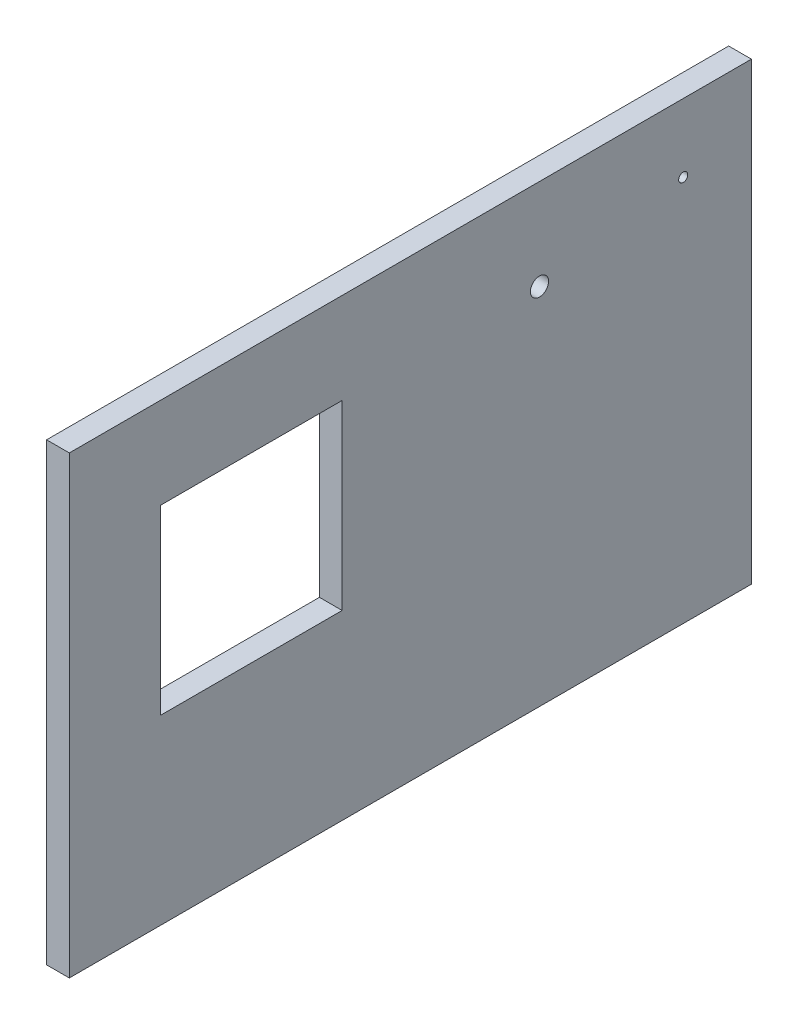
SolidWorks part; units mm, degrees
ref_plane "Front Plane" through (0, 0, 0) normal (0, 0, 1) x (1, 0, 0)
ref_plane "Top Plane" through (0, 0, 0) normal (0, 1, 0) x (1, 0, 0)
ref_plane "Right Plane" through (0, 0, 0) normal (1, 0, 0) x (0, 0, -1)
sketch "Sketch1" plane through (0, 0, 0) normal (1, 0, 0) x (0, 0, -1)
  line L1 (-150, 100) -> (150, 100)
  line L2 (-150, 100) -> (-150, -100)
  line L3 (-150, -100) -> (150, -100)
  line L4 (150, 100) -> (150, -100)
  line L5 (-150, 100) -> (150, -100) construction
  line L6 (-150, -100) -> (150, 100) construction
  point P0 (0, 0)
  dimension "D1" = 300
  dimension "D2" = 200
extrude "Boss-Extrude1" add sketch "Sketch1" along normal blind 10
sketch "Sketch2" plane through (10, 0, 0) normal (1, 0, 0) x (0, 0, -1)
  line L0 (120, 100) -> (120, 70) construction
  line L1 (150, 100) -> (-150, 100) construction
  line L2 (120, 70) -> (150, 70) construction
  line L3 (150, -100) -> (150, 100) construction
  line L4 (80, 100) -> (80, 30) construction
  line L5 (80, 30) -> (150, 30) construction
  line L6 (120, 70) -> (56.7861, 60) construction
  line L7 (-150, -100) -> (150, -100) construction
  circle A0 centre (120, 70) radius 2
  circle A1 centre (56.7861, 60) radius 4
  dimension "D5" = 4
  dimension "D6" = 8
  dimension "D1" = 30
  dimension "D2" = 30
  dimension "D3" = 40
  dimension "D4" = 40
  dimension "D7" = 64
  dimension "D9" = 160
extrude "Cut-Extrude1" cut sketch "Sketch2" against normal blind 10
sketch "Sketch3" plane through (10, 0, 0) normal (1, 0, 0) x (0, 0, -1)
  line L0 (150, 100) -> (-150, 100) construction
  line L1 (-30, -20) -> (-110, -20)
  line L2 (-30, -20) -> (-30, 60)
  line L3 (-30, 60) -> (-110, 60)
  line L4 (-110, -20) -> (-110, 60)
  line L5 (-30, -20) -> (-110, 60) construction
  line L6 (-30, 60) -> (-110, -20) construction
  line L7 (-150, 100) -> (-150, -100) construction
  point P0 (-70, 20)
  dimension "D1" = 40
  dimension "D2" = 40
  dimension "D3" = 80
  dimension "D4" = 80
extrude "Cut-Extrude2" cut sketch "Sketch3" against normal blind 10
